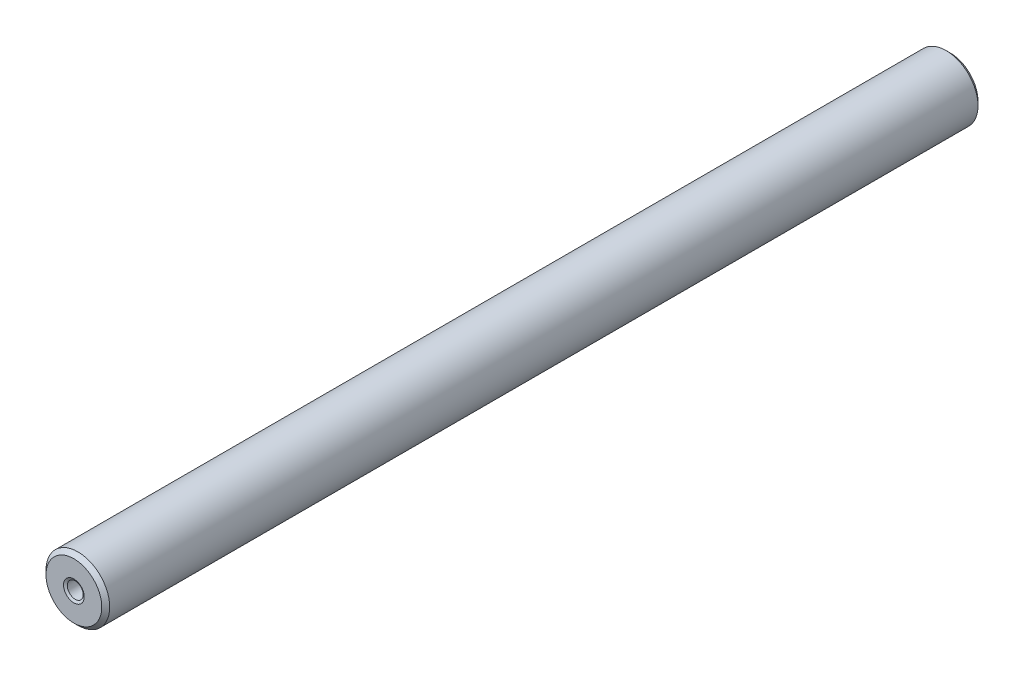
SolidWorks part; units mm, degrees
ref_plane "Front Plane" through (0, 0, 0) normal (0, 0, 1) x (1, 0, 0)
ref_plane "Top Plane" through (0, 0, 0) normal (0, 1, 0) x (1, 0, 0)
ref_plane "Right Plane" through (0, 0, 0) normal (1, 0, 0) x (0, 0, -1)
sketch "Sketch1" plane through (0, 0, 0) normal (0, 1, 0) x (1, 0, 0)
  line L0 (0, 0) -> (0, -110) construction
  line L1 (0, 0) -> (-4, 0) construction
  line L2 (-4, 0) -> (-4, -110) construction
  line L3 (-4, -110) -> (0, -110) construction
  line L4 (-1, 0) -> (-1, -110) construction
  line L5 (0, -2) -> (-4, -2) construction
  line L6 (-1, 0) -> (-4, 0)
  line L7 (0, -55) -> (-4, -55) construction
  line L8 (0, -2) -> (-1, -2)
  line L9 (-1, -2) -> (-1, 0)
  line L10 (0, -108) -> (-1, -108)
  line L11 (-1, -108) -> (-1, -110)
  line L12 (-4, 0) -> (-4, -110)
  line L13 (-4, -110) -> (-1, -110)
  line L14 (0, -108) -> (0, -2)
  dimension "D1" = 110
  dimension "D2" = 4
  dimension "D3" = 1
  dimension "D4" = 2
revolve "Revolve1" add sketch "Sketch1" angle 360 about L14
chamfer "Chamfer1" distance 0.5 angle 45 2 edges at (4, 0, 0) (4, 0, 110)
chamfer "Chamfer2" distance 0.3 angle 30 4 edges at (1, 0, 2) (1, 0, 0) (1, 0, 108) (1, 0, 110)
